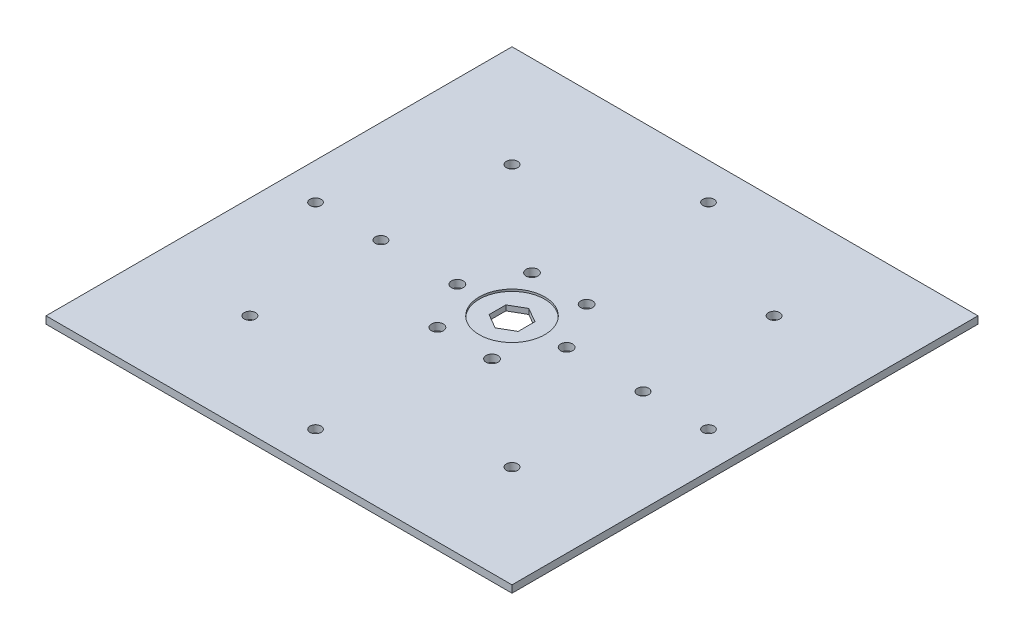
SolidWorks part; units mm, degrees
material "5052-H32"
ref_plane "Front Plane" through (0, 0, 0) normal (0, 0, 1) x (1, 0, 0)
ref_plane "Top Plane" through (0, 0, 0) normal (0, 1, 0) x (1, 0, 0)
ref_plane "Right Plane" through (0, 0, 0) normal (1, 0, 0) x (0, 0, -1)
sketch "Sketch1" plane through (0, 0, 0) normal (0, 1, 0) x (1, 0, 0)
  line L0 (101.6, 93.1218) -> (101.6, -157.5968) construction
  line L1 (0, 0) -> (203.2, 0)
  line L2 (0, 0) -> (0, 203.2)
  line L3 (0, 203.2) -> (203.2, 203.2)
  line L4 (203.2, 0) -> (203.2, 203.2)
  line L5 (-196.9541, 101.6) -> (168.7576, 101.6) construction
  line L6 (44.45, 158.75) -> (44.45, 44.45) construction
  line L7 (89.6938, 122.2222) -> (101.6, 101.6) construction
  line L8 (107.95, 105.2662) -> (101.6, 108.9323)
  line L9 (101.6, 108.9323) -> (95.25, 105.2662)
  line L10 (95.25, 105.2662) -> (95.25, 97.9338)
  line L11 (95.25, 97.9338) -> (101.6, 94.2677)
  line L12 (101.6, 94.2677) -> (107.95, 97.9338)
  line L13 (107.95, 97.9338) -> (107.95, 105.2662)
  line L14 (101.6, 101.6) -> (113.5062, 122.2222) construction
  line L15 (101.6, 101.6) -> (113.5062, 80.9778) construction
  line L16 (89.6938, 80.9778) -> (101.6, 101.6) construction
  line L17 (15.9284, 101.6) -> (101.6, 187.2716) construction
  line L18 (101.6, 187.2716) -> (187.2716, 101.6) construction
  line L19 (187.2716, 101.6) -> (101.6, 15.9284) construction
  line L20 (101.6, 15.9284) -> (15.9284, 101.6) construction
  circle A0 centre (44.45, 158.75) radius 2.4574
  circle A1 centre (44.45, 101.6) radius 2.4574
  circle A2 centre (44.45, 44.45) radius 2.4575
  circle A3 centre (158.75, 44.45) radius 2.4574
  circle A4 centre (158.75, 101.6) radius 2.4575
  circle A5 centre (158.75, 158.75) radius 2.4574
  circle A6 centre (101.6, 101.6) radius 6.35 construction
  circle A7 centre (101.6, 101.6) radius 23.8125 construction
  circle A8 centre (77.7875, 101.6) radius 2.5908
  circle A9 centre (89.6938, 122.2222) radius 2.5908
  circle A10 centre (89.6938, 80.9778) radius 2.5908
  circle A11 centre (113.5062, 122.2222) radius 2.5908
  circle A12 centre (125.4125, 101.6) radius 2.5908
  circle A13 centre (113.5062, 80.9778) radius 2.5908
  circle A14 centre (101.6, 187.2716) radius 2.413
  circle A15 centre (187.2716, 101.6) radius 2.413
  circle A16 centre (101.6, 15.9284) radius 2.413
  circle A17 centre (15.9284, 101.6) radius 2.413
  point P4 (101.6, 203.2)
  point P5 (0, 101.6)
  point P9 (101.6, 203.2)
  point P11 (0, 101.6)
  point P26 (95.25, 101.6)
  point P34 (107.95, 101.6)
  dimension "D5" = 4.9149
  dimension "D6" = 4.9149
  dimension "D7" = 4.9149
  dimension "D8" = 12.7
  dimension "D9" = 47.625
  dimension "D10" = 5.1816
  dimension "D11" = 5.1816
  dimension "D12" = 60
  dimension "D13" = 5.1816
  dimension "D14" = 5.1816
  dimension "D15" = 5.1816
  dimension "D18" = 5.1816
  dimension "D24" = 4.826
  dimension "D25" = 4.826
  dimension "D26" = 4.826
  dimension "D27" = 4.826
  dimension "D1" = 203.2
  dimension "D2" = 203.2
  dimension "D3" = 114.3
  dimension "D4" = 57.15
  dimension "D16" = 60
  dimension "D17" = 60
  dimension "D19" = 120
  dimension "D20" = 121.158
  dimension "D21" = 121.158
  dimension "D22" = 121.158
  dimension "D23" = 90
extrude "Boss-Extrude1" add sketch "Sketch1" along normal blind 3.175
sketch "Sketch2" plane through (0, 3.175, 0) normal (0, 1, 0) x (1, 0, 0)
  circle A0 centre (101.6, 101.6) radius 14.2875
  dimension "D3" = 28.575
  dimension "D1" = 101.6
  dimension "D2" = 101.6
extrude "Cut-Extrude1" cut sketch "Sketch2" against normal blind 0.889
